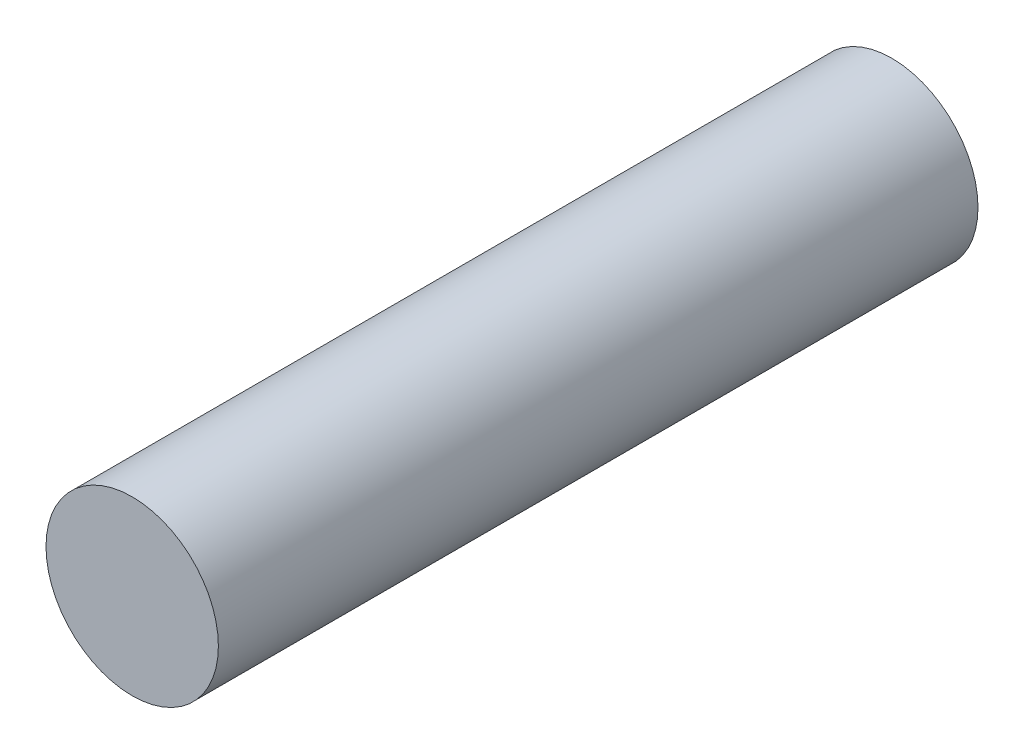
SolidWorks part; units mm, degrees
ref_plane "Front Plane" through (0, 0, 0) normal (0, 0, 1) x (1, 0, 0)
ref_plane "Top Plane" through (0, 0, 0) normal (0, 1, 0) x (1, 0, 0)
ref_plane "Right Plane" through (0, 0, 0) normal (1, 0, 0) x (0, 0, -1)
sketch "Sketch1" plane through (0, 0, 0) normal (0, 0, 1) x (1, 0, 0)
  circle A0 centre (0, 0) radius 2.95
  dimension "D1" = 5.9
extrude "Boss-Extrude1" add sketch "Sketch1" along normal blind 26
